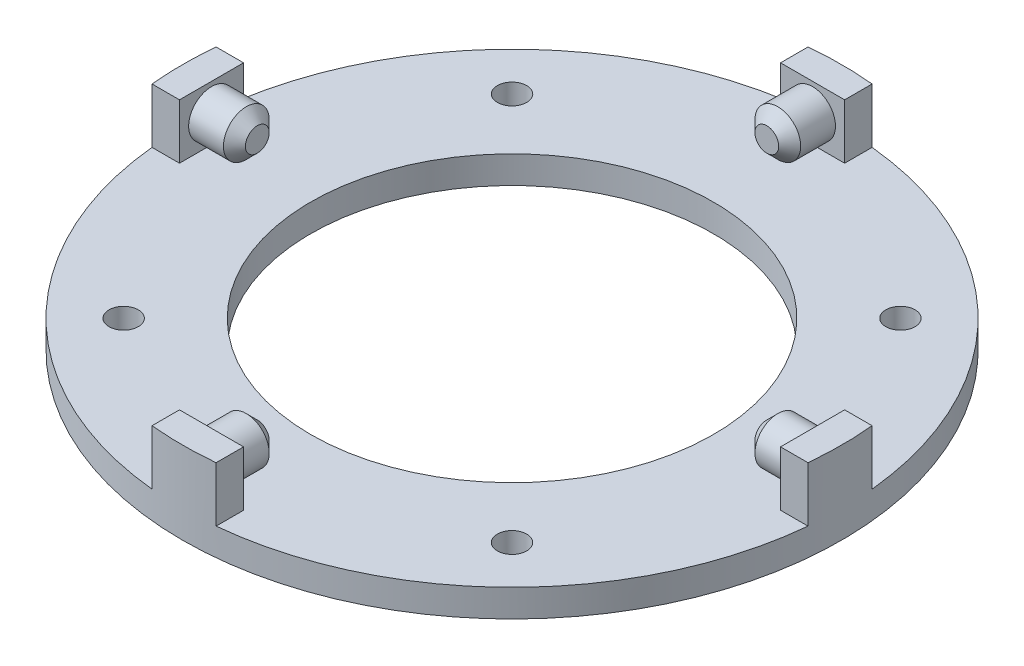
SolidWorks part; units mm, degrees
ref_plane "Front Plane" through (0, 0, 0) normal (0, 0, 1) x (1, 0, 0)
ref_plane "Top Plane" through (0, 0, 0) normal (0, 1, 0) x (1, 0, 0)
ref_plane "Right Plane" through (0, 0, 0) normal (1, 0, 0) x (0, 0, -1)
sketch "Sketch1" plane through (0, 0, 0) normal (0, 1, 0) x (1, 0, 0)
  circle A0 centre (0, 0) radius 22
  circle A1 centre (0, 0) radius 36
  dimension "D1" = 44
  dimension "D2" = 72
extrude "Boss-Extrude1" add sketch "Sketch1" along normal blind 3
sketch "Sketch2" plane through (0, 3, 0) normal (0, 1, 0) x (1, 0, 0)
  line L1 (-32.8295, 3.5) -> (-35.8295, 3.5)
  line L2 (-32.8295, 3.5) -> (-32.8295, -3.5)
  line L3 (-32.8295, -3.5) -> (-35.8295, -3.5)
  line L5 (-32.8295, 3.5) -> (-35.8295, -3.5) construction
  line L6 (-32.8295, -3.5) -> (-35.8295, 3.5) construction
  circle A0 centre (0, 0) radius 36 construction
  arc A1 (-35.8295, 3.5) -> (-35.8295, -3.5) centre (0, 0) ccw
  point P0 (-34.3295, 0)
  point P5 (0, 0)
  point P8 (-34.7847, -3.5895)
  point P9 (0, 0)
  dimension "D1" = 3
  dimension "D2" = 7
extrude "Boss-Extrude2" add sketch "Sketch2" along normal blind 6
sketch "Sketch3" plane through (-32.8295, 0, 0) normal (1, 0, 0) x (0, 0, -1)
  line L0 (22, 3) -> (-22, 3) construction
  circle A0 centre (0, 6) radius 2.5
  point P2 (0, 0)
  point P6 (0, 0)
  dimension "D1" = 5
  dimension "D2" = 3
extrude "Boss-Extrude3" add sketch "Sketch3" along normal blind 5
chamfer "Chamfer1" distance 1.2 angle 45 1 edges at (-27.8295, 6, -2.5)
pattern_circular "CirPattern1" count 4 over 360 about axis through (0, 0, 0) along (0, 1, 0) of "Boss-Extrude2", "Boss-Extrude3", "Chamfer1"
sketch "Sketch4" plane through (0, 3, 0) normal (0, 1, 0) x (1, 0, 0)
  line L0 (0, 36) -> (0, 0) construction
  line L1 (0, 0) -> (-15.5563, 15.5563) construction
  arc A0 (3.5, 35.8295) -> (-3.5, 35.8295) centre (0, 0) ccw construction
  circle A1 centre (0, 0) radius 22 construction
  circle A2 centre (-21.2132, 21.2132) radius 1.6
  dimension "D2" = 3.2
  dimension "D1" = 45
  dimension "D3" = 30
extrude "Cut-Extrude1" cut sketch "Sketch4" against normal up to next (3 mm away)
pattern_circular "CirPattern2" count 4 over 360 about axis through (0, 0, 0) along (0, 1, 0) of "Cut-Extrude1"
